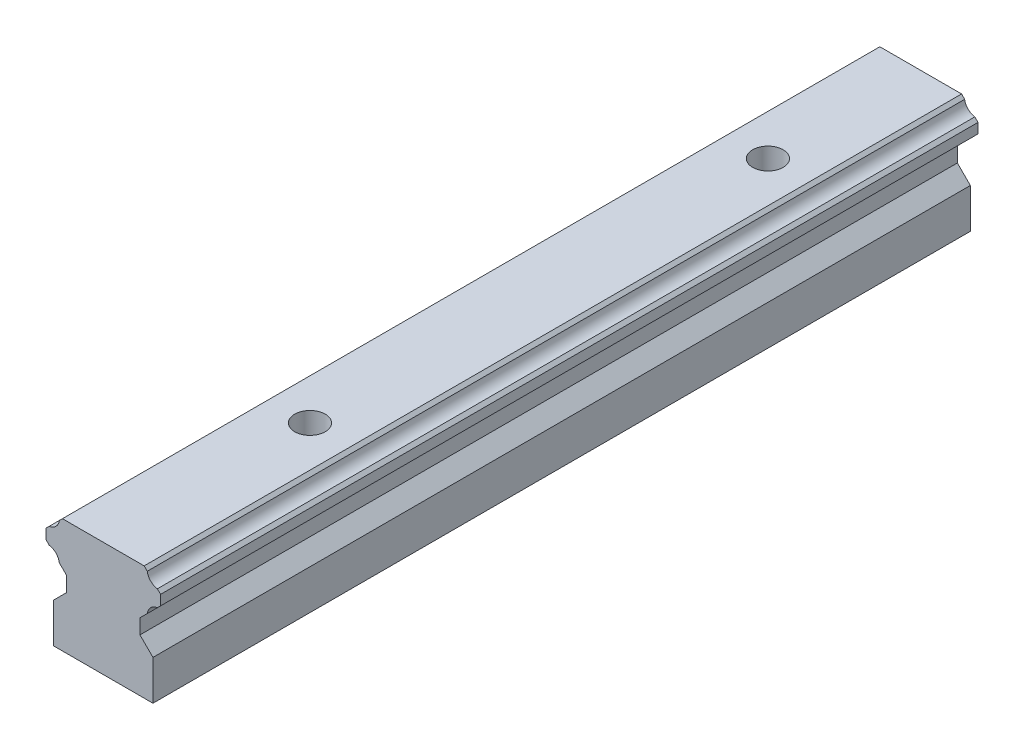
SolidWorks part; units mm, degrees
ref_plane "Front Plane" through (0, 0, 0) normal (0, 0, 1) x (1, 0, 0)
ref_plane "Top Plane" through (0, 0, 0) normal (0, 1, 0) x (1, 0, 0)
ref_plane "Right Plane" through (0, 0, 0) normal (1, 0, 0) x (0, 0, -1)
sketch "Sketch1" plane through (0, 0, 0) normal (0, 0, 1) x (1, 0, 0)
  line B0 (-6.5, 0) -> (6.5, 0)
  line B1 (-6.5, 5.2) -> (-6.5, 0)
  line B2 (6.5, 5.2) -> (6.5, 0)
  line B3 (-6.5, 5.2) -> (-4.8, 6.9)
  line B4 (-4.8, 6.9) -> (-4.8, 8.84)
  line B5 (-4.8, 8.84) -> (-5.7549, 9.7949)
  line B6 (-7.0851, 11.1251) -> (-7.5, 11.54)
  line B7 (-7.5, 11.54) -> (-7.5, 12.85)
  line B8 (-7.5, 12.85) -> (-7.0816, 13.2684)
  line B9 (-5.7554, 14.5946) -> (-5.35, 15)
  line B10 (-5.35, 15) -> (5.35, 15)
  line B11 (5.35, 15) -> (5.7554, 14.5946)
  line B12 (7.0816, 13.2684) -> (7.5, 12.85)
  line B13 (7.5, 12.85) -> (7.5, 11.54)
  line B14 (7.5, 11.54) -> (7.0851, 11.1251)
  line B15 (5.7549, 9.7949) -> (4.8, 8.84)
  line B16 (4.8, 8.84) -> (4.8, 6.9)
  line B17 (4.8, 6.9) -> (6.5, 5.2)
  arc B18 (-5.7549, 9.7949) -> (-7.0851, 11.1251) centre (-7.3, 9.58) ccw
  arc B19 (-7.0816, 13.2684) -> (-5.7554, 14.5946) centre (-7.3, 14.813) ccw
  arc B20 (5.7554, 14.5946) -> (7.0816, 13.2684) centre (7.3, 14.813) ccw
  arc B21 (7.0851, 11.1251) -> (5.7549, 9.7949) centre (7.3, 9.58) ccw
sketch_block_instance "Block-RailTopography-1"
sketch_block "Block-RailTopography" parameters "D1"=15
extrude "Boss-Extrude1" add sketch "Sketch1" along normal blind 107
sketch "Sketch2" plane through (0, 15, 0) normal (0, 1, 0) x (1, 0, 0)
  line L0 (0, -1000) -> (0, 49000) construction
  line L1 (5.35, 0) -> (-5.35, 0) construction
  circle A0 centre (0, -20) radius 2
  circle A1 centre (0, -79.944) radius 2
  dimension "D1" = 4
  dimension "D2" = 20
  dimension "D3" = 2
extrude "Cut-Extrude1" cut sketch "Sketch2" against normal through all
